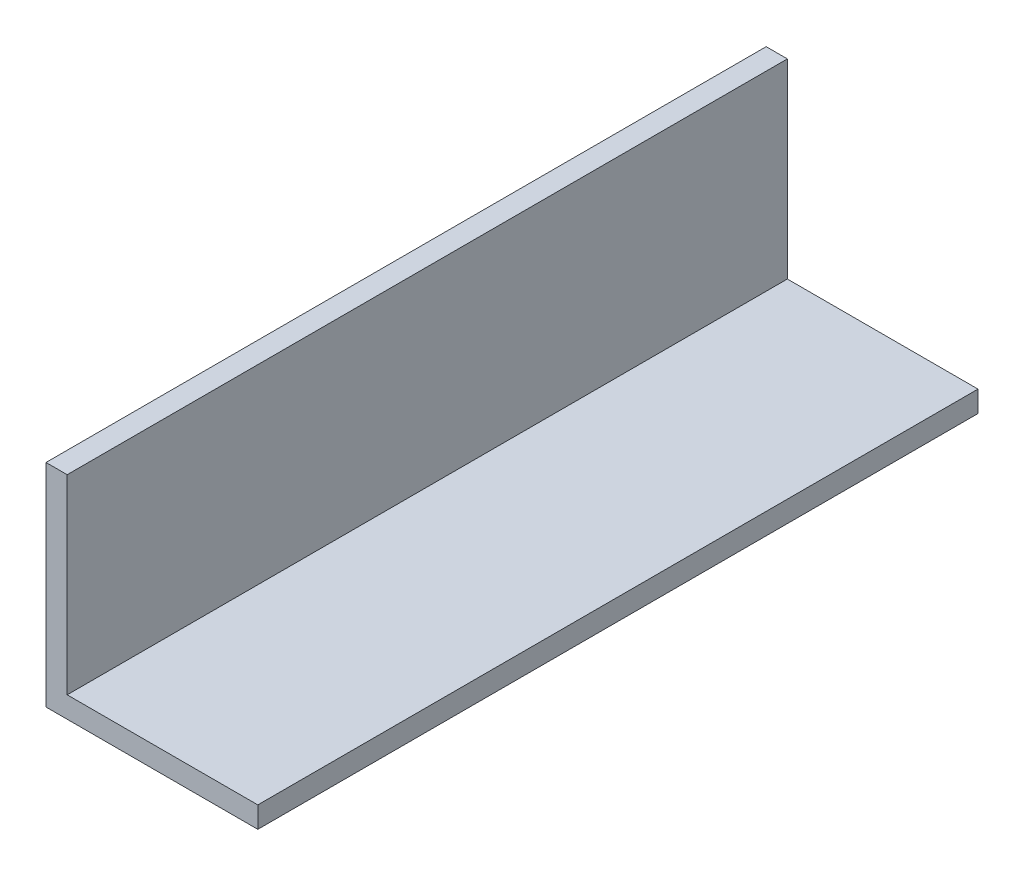
SolidWorks part; units mm, degrees
ref_plane "Front Plane" through (0, 0, 0) normal (0, 0, 1) x (1, 0, 0)
ref_plane "Top Plane" through (0, 0, 0) normal (0, 1, 0) x (1, 0, 0)
ref_plane "Right Plane" through (0, 0, 0) normal (1, 0, 0) x (0, 0, -1)
sketch "Sketch1" plane through (0, 0, 0) normal (0, 0, 1) x (1, 0, 0)
  line L0 (0, 0) -> (20, 0)
  line L4 (2, 20) -> (0, 20)
  line L5 (0, 20) -> (0, 0)
  line L6 (2, 20) -> (2, 2)
  line L7 (2, 2) -> (20, 2)
  line L8 (20, 2) -> (20, 0)
  dimension "D1" = 20
  dimension "D2" = 20
  dimension "D3" = 2
  dimension "D4" = 2
extrude "Boss-Extrude1" add sketch "Sketch1" along normal blind 68
